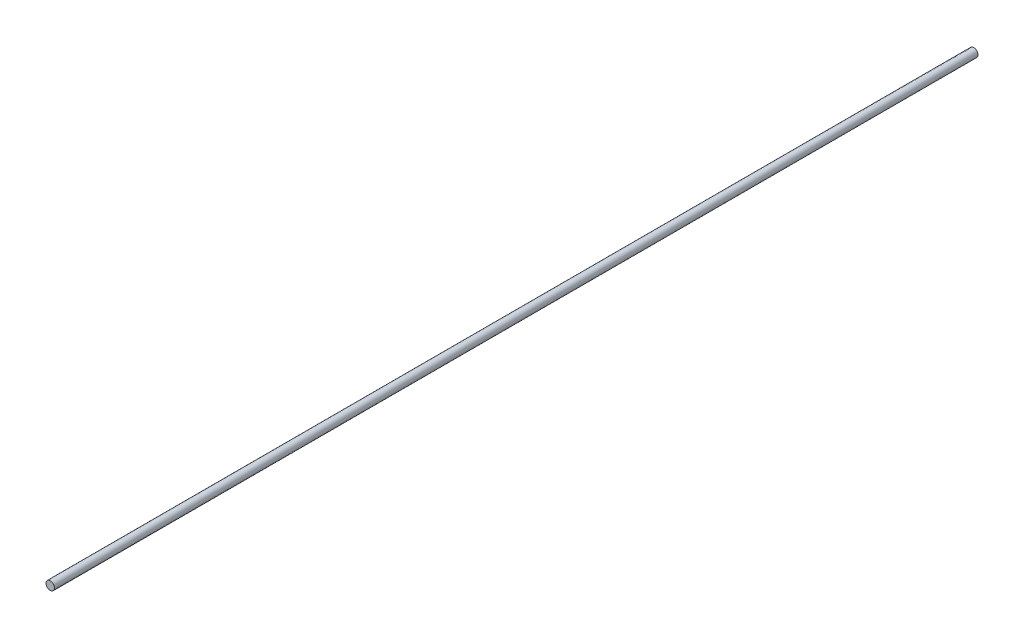
SolidWorks part; units mm, degrees
material "Brass"
ref_plane "Front Plane" through (0, 0, 0) normal (0, 0, 1) x (1, 0, 0)
ref_plane "Top Plane" through (0, 0, 0) normal (0, 1, 0) x (1, 0, 0)
ref_plane "Right Plane" through (0, 0, 0) normal (1, 0, 0) x (0, 0, -1)
sketch "Sketch1" plane through (0, 0, 0) normal (0, 0, 1) x (1, 0, 0)
  circle A0 centre (0, 0) radius 4
extrude "Boss-Extrude2" add sketch "Sketch1" along normal blind 875
